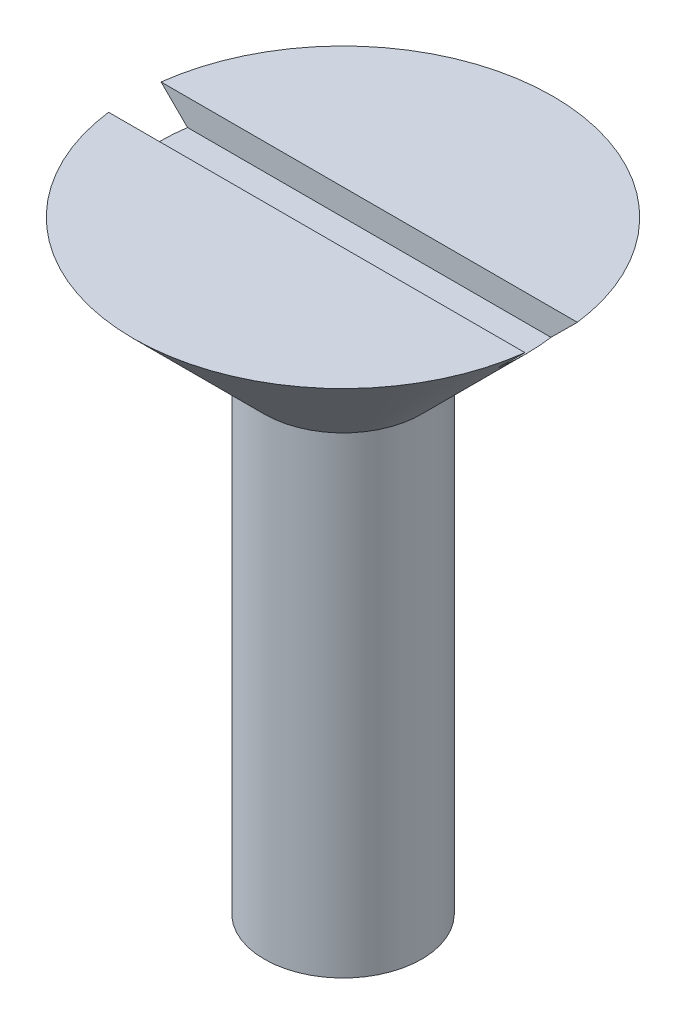
SolidWorks part; units mm, degrees
ref_plane "Front Plane" through (0, 0, 0) normal (0, 0, 1) x (1, 0, 0)
ref_plane "Top Plane" through (0, 0, 0) normal (0, 1, 0) x (1, 0, 0)
ref_plane "Right Plane" through (0, 0, 0) normal (1, 0, 0) x (0, 0, -1)
sketch "Sketch1" plane through (0, 0, 0) normal (0, 0, 1) x (1, 0, 0)
  line L0 (0, 9) -> (0, -9)
  line L3 (3, -9) -> (3, 9)
  line L4 (0, -9) -> (0, -10.7321)
  line L5 (3, -9) -> (0, -10.7321)
  line L6 (0, 9) -> (0, 14)
  line L7 (0, 14) -> (8, 14)
  line L8 (3, 9) -> (8, 14)
  point P4 (0, 0)
  dimension "D1" = 60
  dimension "D2" = 18
  dimension "D3" = 45
  dimension "D4" = 3
revolve "Revolve1" add sketch "Sketch1" angle 360 about L0
sketch "Sketch2" plane through (0, 0, 0) normal (1, 0, 0) x (0, 0, -1)
  line L0 (0, 14) -> (1, 14)
  line L1 (8, 14) -> (-8, 14) construction
  line L2 (0, 14) -> (-1, 14)
  line L3 (-1, 14) -> (-1, 13)
  line L4 (-1, 13) -> (1, 13)
  line L5 (1, 13) -> (1, 14)
extrude "Cut-Extrude1" cut sketch "Sketch2" against normal mid plane 18
